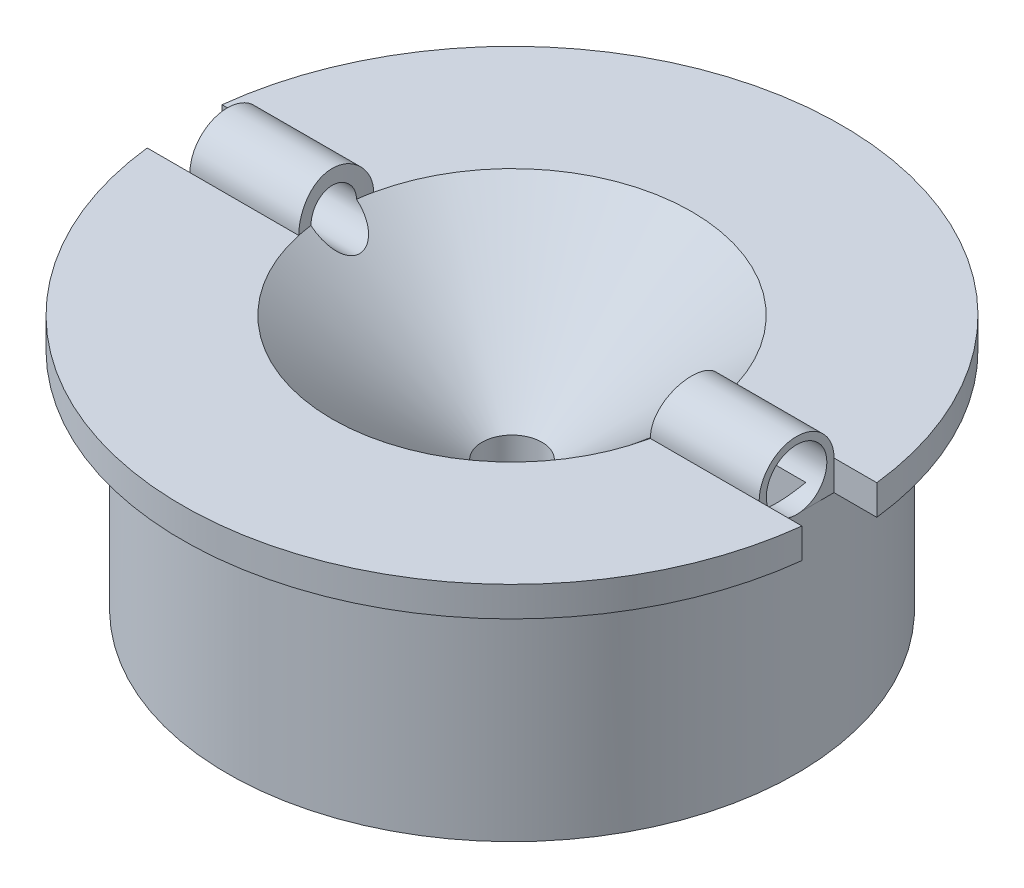
SolidWorks part; units mm, degrees
ref_plane "Front Plane" through (0, 0, 0) normal (0, 0, 1) x (1, 0, 0)
ref_plane "Top Plane" through (0, 0, 0) normal (0, 1, 0) x (1, 0, 0)
ref_plane "Right Plane" through (0, 0, 0) normal (1, 0, 0) x (0, 0, -1)
sketch "Sketch1" plane through (0, 0, 0) normal (0, 0, 1) x (1, 0, 0)
  line L0 (0, 0) -> (12, 0) construction
  line L1 (12, 0) -> (12, 10) construction
  line L2 (0, 0) -> (12, 10)
  line L3 (12, 10) -> (17, 10)
  line L4 (19, 8) -> (19, -7)
  line L5 (19, -7) -> (0, -7)
  line L6 (0, -7) -> (0, 0)
  line L7 (17, 10) -> (22, 10)
  line L8 (22, 10) -> (22, 8)
  line L9 (22, 8) -> (19, 8)
revolve "Revolve1" add sketch "Sketch1" angle 360 about L6
sketch "Sketch2" plane through (0, 10, 0) normal (0, 1, 0) x (1, 0, 0)
  line L0 (0, 0) -> (17, 0) construction
  line L1 (19, 0) -> (12, 0)
  line L2 (12, 0) -> (12, 2.5)
  line L3 (19, 0) -> (19, 2.5)
  line L4 (-12, 0) -> (-19, 0)
  line L5 (-19, 0) -> (-19, 2.5)
  line L6 (-12, 0) -> (-12, 2.5)
  line L7 (-12, 2.5) -> (-19, 2.5)
  line L8 (12, 2.5) -> (19, 2.5)
  circle A2 centre (0, 0) radius 19 construction
  circle A6 centre (0, 0) radius 12 construction
revolve "Revolve2" add sketch "Sketch2" angle 180 about L0
sketch "Sketch8" plane through (-12, 0, 0) normal (1, 0, 0) x (0, 0, -1)
  line L2 (-2.5, 10) -> (0, 10)
  line L3 (0, 10) -> (2.5, 10)
  line L4 (-2.5, 10) -> (0, 10)
  line L5 (0, 10) -> (2.5, 10)
  arc A1 (2.5, 10) -> (-2.5, 10) centre (0, 10) ccw
  arc A2 (2.5, 10) -> (-2.5, 10) centre (0, 10) ccw
  dimension "D1" = 0
extrude "Boss-Extrude4" add sketch "Sketch8" along normal up to surface (24 mm away) up to face at (12, 10.8333, 0)
sketch "Sketch9" plane through (0, 10, 0) normal (0, 1, 0) x (1, 0, 0)
  arc A0 (-11.7367, 2.5) -> (-11.7367, -2.5) centre (0, 0) ccw construction
  arc A1 (11.7367, -2.5) -> (11.7367, 2.5) centre (0, 0) ccw construction
  arc A2 (-11.7367, 2.5) -> (-11.7367, -2.5) centre (0, 0) ccw
  arc A3 (11.7367, -2.5) -> (11.7367, 2.5) centre (0, 0) ccw
  arc A4 (11.7367, 2.5) -> (-11.7367, 2.5) centre (0, 0) ccw construction
  arc A5 (-11.7367, -2.5) -> (11.7367, -2.5) centre (0, 0) ccw construction
  arc A6 (11.7367, 2.5) -> (-11.7367, 2.5) centre (0, 0) ccw
  arc A7 (-11.7367, -2.5) -> (11.7367, -2.5) centre (0, 0) ccw
extrude "Cut-Extrude1" cut sketch "Sketch9" along normal through all
sketch "Sketch17" plane through (0, 10, 0) normal (0, 1, 0) x (1, 0, 0)
  line L1 (19, 2.5) -> (22, 2.5)
  line L2 (19, 2.5) -> (19, -2.5)
  line L3 (19, -2.5) -> (22, -2.5)
  line L4 (22, 2.5) -> (22, -2.5)
  line L5 (-19, 2.5) -> (-22, 2.5)
  line L6 (-19, 2.5) -> (-19, -2.5)
  line L7 (-19, -2.5) -> (-22, -2.5)
  line L8 (-22, 2.5) -> (-22, -2.5)
extrude "Cut-Extrude6" cut sketch "Sketch17" against normal through all
sketch "Sketch16" plane through (-19, 0, 0) normal (-1, 0, 0) x (0, 0, 1)
  line L0 (2.5, 10) -> (-2.5, 10) construction
  circle A0 centre (0, 10) radius 1.52
extrude "Cut-Extrude5" cut sketch "Sketch16" against normal through all and the other way through all
sketch "Sketch19" plane through (-19, 0, 0) normal (-1, 0, 0) x (0, 0, 1)
  circle A0 centre (0, 10) radius 2.02
extrude "Cut-Extrude7" cut sketch "Sketch19" against normal blind 3
sketch "Sketch20" plane through (19, 0, 0) normal (1, 0, 0) x (0, 0, -1)
  circle A0 centre (0, 10) radius 2.02
extrude "Cut-Extrude8" cut sketch "Sketch20" against normal blind 3
sketch "Sketch21" plane through (0, -7, 0) normal (0, -1, 0) x (1, 0, 0)
  circle A0 centre (0, 0) radius 15
extrude "Cut-Extrude9" cut sketch "Sketch21" against normal blind 6.5
sketch "Sketch22" plane through (0, -0.5, 0) normal (0, -1, 0) x (1, 0, 0)
  circle A0 centre (0, 0) radius 5
extrude "Boss-Extrude6" add sketch "Sketch22" along normal blind 6.5
sketch "Sketch23" plane through (0, -0.5, 0) normal (0, -1, 0) x (1, 0, 0)
  line L0 (0, 0) -> (10, 0) construction
  line L1 (10, -1.5) -> (12, -1.5)
  line L2 (10, -1.5) -> (10, 1.5)
  line L3 (12, -1.5) -> (12, 1.5)
  line L4 (12, 1.5) -> (10, 1.5)
sketch3d "3DSketch3"
  line L1 (10, -0.5, 0) -> (16, 8.48, 0)
  line L2 (16, 8.48, 0) -> (16.8132, 9.6971, 0)
  circle A0 centre (16, 10, 0) radius 1.52 construction
  point P5 (14.48, 10, 0)
sweep "Cut-Sweep2" cut profiles "Sketch23" path "3DSketch3"
sketch "Sketch24" plane through (0, -0.5, 0) normal (0, -1, 0) x (1, 0, 0)
  line L0 (0, 0) -> (-10, 0) construction
  line L1 (-10, -1.5) -> (-10, 1.5)
  line L2 (-10, -1.5) -> (-12, -1.5)
  line L3 (-12, -1.5) -> (-12, 1.5)
  line L4 (-12, 1.5) -> (-10, 1.5)
sketch3d "3DSketch4"
  line L1 (-10, -0.5, 0) -> (-16, 8.48, 0)
  line L2 (-16, 8.48, 0) -> (-16.8132, 9.6971, 0)
  circle A0 centre (-16, 10, 0) radius 1.52 construction
  point P5 (-14.48, 10, 0)
sweep "Cut-Sweep3" cut profiles "Sketch24" path "3DSketch4"
sketch "Sketch25" plane through (0, -7, 0) normal (0, -1, 0) x (1, 0, 0)
  circle A0 centre (0, 0) radius 2
extrude "Cut-Extrude11" cut sketch "Sketch25" against normal through all
sketch "Sketch26" plane through (0, -7, 0) normal (0, -1, 0) x (1, 0, 0)
  circle A0 centre (0, 0) radius 3.17
extrude "Cut-Extrude12" cut sketch "Sketch26" against normal up to surface (6.5 mm away) up to face at (-11, -0.5, 0)
